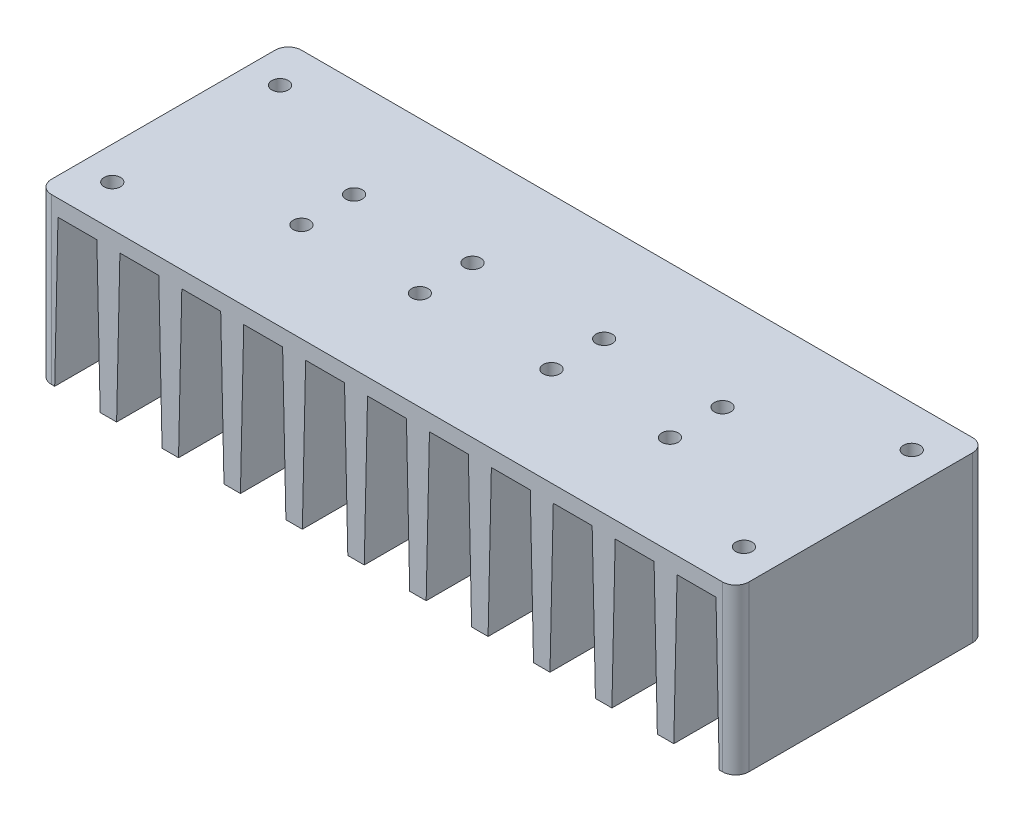
SolidWorks part; units mm, degrees
ref_plane "Front Plane" through (0, 0, 0) normal (0, 0, 1) x (1, 0, 0)
ref_plane "Top Plane" through (0, 0, 0) normal (0, 1, 0) x (1, 0, 0)
ref_plane "Right Plane" through (0, 0, 0) normal (1, 0, 0) x (0, 0, -1)
sketch "Sketch1" plane through (0, 0, 0) normal (0, 1, 0) x (1, 0, 0)
  line L1 (-106, -38) -> (106, -38)
  line L2 (-106, -38) -> (-106, 38)
  line L3 (-106, 38) -> (106, 38)
  line L4 (106, -38) -> (106, 38)
  line L5 (-106, -38) -> (106, 38) construction
  line L6 (-106, 38) -> (106, -38) construction
  point P0 (0, 0)
  dimension "D1" = 212
  dimension "D2" = 76
extrude "Boss-Extrude1" add sketch "Sketch1" along normal blind 50
sketch "Sketch2" plane through (0, 0, 38) normal (0, 0, 1) x (1, 0, 0)
  line L0 (101, 0) -> (100, 45)
  line L1 (-106, 0) -> (106, 0) construction
  line L2 (100, 45) -> (88.1818, 45)
  line L3 (88.1818, 45) -> (87.1818, 0)
  line L4 (68.3636, 0) -> (82.1818, 0)
  line L5 (87.1818, 0) -> (101, 0)
  line L6 (-106, 50) -> (106, 50) construction
  line L7 (82.1818, 0) -> (81.1818, 45)
  line L8 (81.1818, 45) -> (69.3636, 45)
  line L9 (69.3636, 45) -> (68.3636, 0)
  line L10 (49.5455, 0) -> (63.3636, 0)
  line L11 (63.3636, 0) -> (62.3636, 45)
  line L12 (62.3636, 45) -> (50.5455, 45)
  line L13 (50.5455, 45) -> (49.5455, 0)
  line L14 (30.7273, 0) -> (44.5455, 0)
  line L15 (44.5455, 0) -> (43.5455, 45)
  line L16 (43.5455, 45) -> (31.7273, 45)
  line L17 (31.7273, 45) -> (30.7273, 0)
  line L18 (11.9091, 0) -> (25.7273, 0)
  line L19 (25.7273, 0) -> (24.7273, 45)
  line L20 (24.7273, 45) -> (12.9091, 45)
  line L21 (12.9091, 45) -> (11.9091, 0)
  line L22 (-6.9091, 0) -> (6.9091, 0)
  line L23 (6.9091, 0) -> (5.9091, 45)
  line L24 (5.9091, 45) -> (-5.9091, 45)
  line L25 (-5.9091, 45) -> (-6.9091, 0)
  line L26 (-25.7273, 0) -> (-11.9091, 0)
  line L27 (-11.9091, 0) -> (-12.9091, 45)
  line L28 (-12.9091, 45) -> (-24.7273, 45)
  line L29 (-24.7273, 45) -> (-25.7273, 0)
  line L30 (-44.5454, 0) -> (-30.7273, 0)
  line L31 (-30.7273, 0) -> (-31.7273, 45)
  line L32 (-31.7273, 45) -> (-43.5454, 45)
  line L33 (-43.5454, 45) -> (-44.5454, 0)
  line L34 (-63.3636, 0) -> (-49.5454, 0)
  line L35 (-49.5454, 0) -> (-50.5454, 45)
  line L36 (-50.5454, 45) -> (-62.3636, 45)
  line L37 (-62.3636, 45) -> (-63.3636, 0)
  line L38 (-82.1818, 0) -> (-68.3636, 0)
  line L39 (-68.3636, 0) -> (-69.3636, 45)
  line L40 (-69.3636, 45) -> (-81.1818, 45)
  line L41 (-81.1818, 45) -> (-82.1818, 0)
  line L42 (-101, 0) -> (-87.1818, 0)
  line L43 (-87.1818, 0) -> (-88.1818, 45)
  line L44 (-88.1818, 45) -> (-100, 45)
  line L45 (-100, 45) -> (-101, 0)
  dimension "D1" = 5
  dimension "D2" = 13.8182
  dimension "D3" = 1
  dimension "D4" = 1
  dimension "D5" = 5
  dimension "D7" = 5
  dimension "D6" = 11
extrude "Cut-Extrude1" cut sketch "Sketch2" against normal blind 77
sketch "Sketch4" plane through (0, 50, 0) normal (0, 1, 0) x (1, 0, 0)
  line L0 (-27.5, 0) -> (27.5, 0) construction
  line L1 (0, -27.5) -> (0, 27.5) construction
  circle A0 centre (-96, 25.5) radius 2.5
  circle A1 centre (-96, -25.5) radius 2.5
  circle A2 centre (96, 25.5) radius 2.5
  circle A3 centre (96, -25.5) radius 2.5
  circle A4 centre (-56, 8) radius 2.5
  circle A5 centre (-20, 8) radius 2.5
  circle A7 centre (-20, -8) radius 2.5
  circle A8 centre (-56, -8) radius 2.5
  circle A9 centre (56, -8) radius 2.5
  circle A10 centre (20, -8) radius 2.5
  circle A11 centre (20, 8) radius 2.5
  circle A12 centre (56, 8) radius 2.5
  dimension "D1" = 96
  dimension "D5" = 5
  dimension "D6" = 5
  dimension "D7" = 96
  dimension "D11" = 5
  dimension "D12" = 5
  dimension "D13" = 20
  dimension "D16" = 5
  dimension "D17" = 5
  dimension "D2" = 96
  dimension "D3" = 25.5
  dimension "D4" = 25.5
  dimension "D8" = 25.5
  dimension "D9" = 25.5
  dimension "D10" = 96
  dimension "D14" = 56
  dimension "D15" = 8
extrude "Cut-Extrude2" cut sketch "Sketch4" against normal blind 77
fillet "Fillet1" radius 4 4 edges at (-106, 25, -38) (-106, 25, 38) (106, 25, -38) (106, 25, 38)
